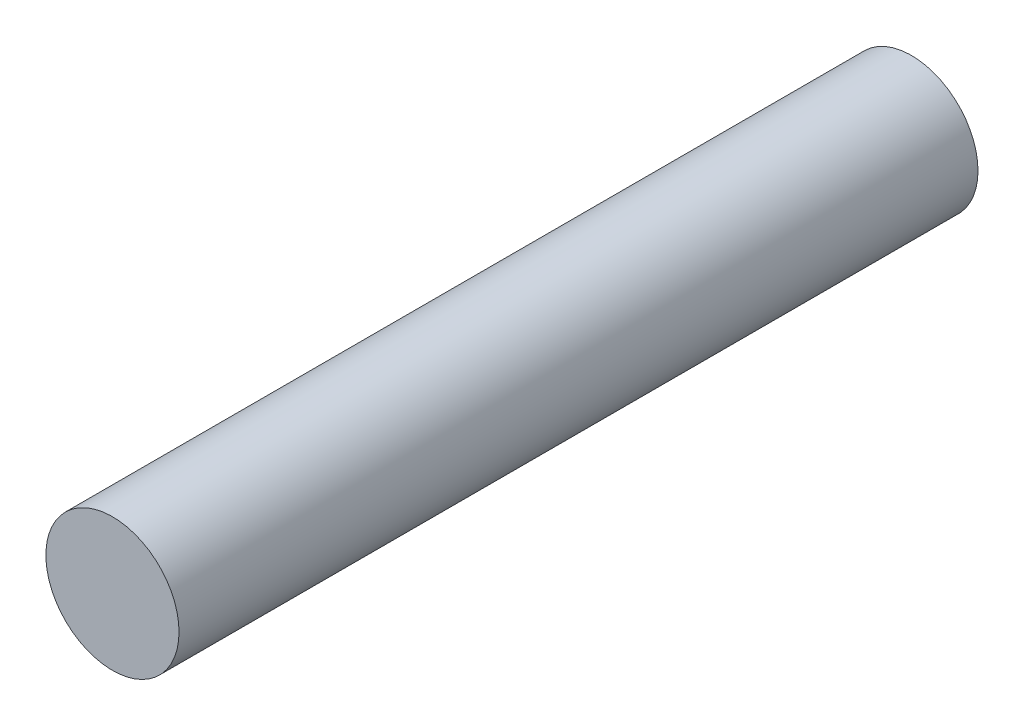
SolidWorks part; units mm, degrees
ref_plane "Ön Düzlem" through (0, 0, 0) normal (0, 0, 1) x (1, 0, 0)
ref_plane "Üst Düzlem" through (0, 0, 0) normal (0, 1, 0) x (1, 0, 0)
ref_plane "Sağ Düzlem" through (0, 0, 0) normal (1, 0, 0) x (0, 0, -1)
sketch "Sketch1" plane through (0, 0, 0) normal (0, 0, 1) x (1, 0, 0)
  circle A0 centre (0, 0) radius 2.5
extrude "Boss-Extrude1" add sketch "Sketch1" along normal blind 30
